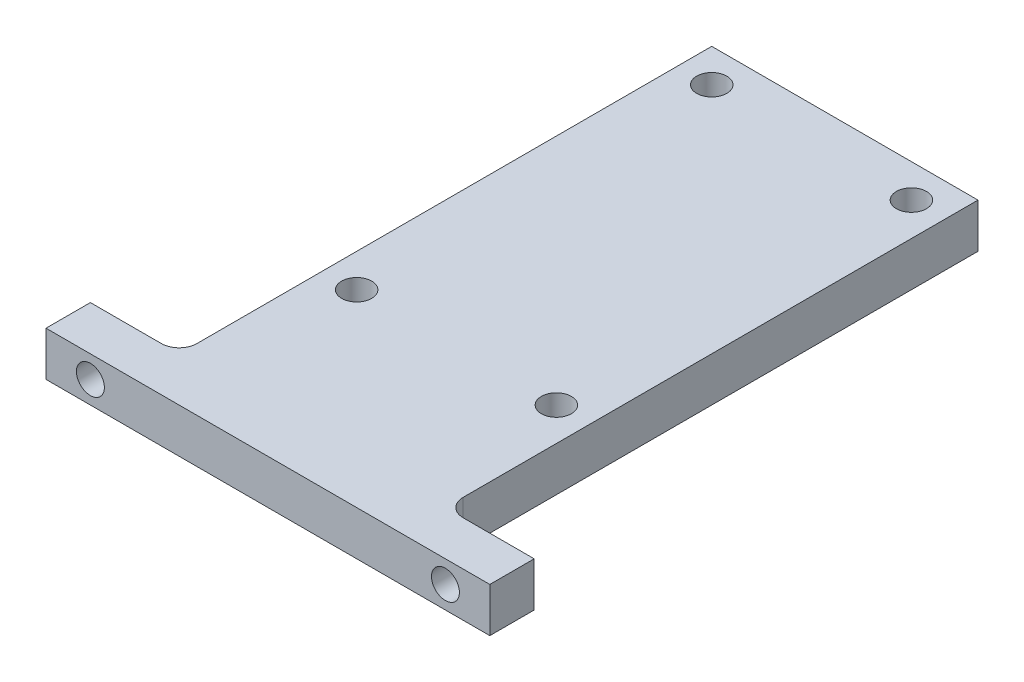
SolidWorks part; units mm, degrees
ref_plane "Front Plane" through (0, 0, 0) normal (0, 0, 1) x (1, 0, 0)
ref_plane "Top Plane" through (0, 0, 0) normal (0, 1, 0) x (1, 0, 0)
ref_plane "Right Plane" through (0, 0, 0) normal (1, 0, 0) x (0, 0, -1)
sketch "Sketch1" plane through (0, 0, 0) normal (0, 1, 0) x (1, 0, 0)
  line L0 (0, 0) -> (63.5, 0)
  line L1 (63.5, 0) -> (63.5, 6.35)
  line L2 (63.5, 6.35) -> (50.8, 6.35)
  line L3 (50.8, 6.35) -> (50.8, 82.55)
  line L4 (50.8, 82.55) -> (12.7, 82.55)
  line L5 (12.7, 82.55) -> (12.7, 6.35)
  line L6 (12.7, 6.35) -> (0, 6.35)
  line L7 (0, 6.35) -> (0, 0)
  dimension "D1" = 12.7
  dimension "D2" = 38.1
  dimension "D3" = 76.2
  dimension "D4" = 6.35
extrude "Boss-Extrude1" add sketch "Sketch1" along normal blind 6.35
sketch "Sketch2" plane through (0, 0, 0) normal (0, 0, 1) x (1, 0, 0)
  line L0 (0, 6.35) -> (0, 0) construction
  line L1 (12.7, 6.35) -> (0, 6.35) construction
  line L2 (63.5, 6.35) -> (50.8, 6.35) construction
  circle A0 centre (6.35, 3.175) radius 2
  circle A1 centre (57.15, 3.175) radius 2
  point P7 (0, 3.175)
  point P11 (6.35, 6.35)
  point P15 (57.15, 6.35)
  dimension "D1" = 4
extrude "Cut-Extrude1" cut sketch "Sketch2" against normal through all both and the other way through all
sketch "Sketch3" plane through (0, 6.35, 0) normal (0, 1, 0) x (1, 0, 0)
  line L3 (12.7, 82.55) -> (12.7, 6.35) construction
  line L4 (50.8, 82.55) -> (12.7, 82.55) construction
  point P0 (17.4625, 77.7875)
  point P5 (17.4625, 26.9875)
  point P6 (46.0375, 77.7875)
  point P7 (46.0375, 26.9875)
  point P8 (0, 0)
  point P9 (0, 0)
  point P10 (0, 0)
  dimension "D1" = 4.7625
  dimension "D2" = 4.7625
  dimension "D3" = 50.8
  dimension "D4" = 28.575
fillet "Fillet1" radius 2.54 2 edges at (12.7, 3.175, -6.35) (50.8, 3.175, -6.35)
hole_wizard "M4 Clearance Hole1" positions "Sketch4" profile "Sketch5" hole size "M4" standard "ANSI Metric" end condition through all
sketch "Sketch4" plane through (0, 6.35, 0) normal (0, 1, 0) x (1, 0, 0)
  point P0 (17.4625, 77.7875)
  point P3 (46.0375, 77.7875)
  point P6 (46.0375, 26.9875)
  point P9 (17.4625, 26.9875)
sketch "Sketch5" plane through (17.4625, 6.35, -77.7875) normal (1, 0, 0) x (0, 0, 1)
  line L0 (0, 0) -> (0, 6.35)
  line L1 (0, 6.35) -> (2.15, 6.35)
  line L2 (2.15, 6.35) -> (2.15, 0)
  line L5 (2.15, 0) -> (0, 0)
  line L11 (0, -6.35) -> (0, 107.95) construction
  dimension "Thru Hole Dia." = 4.3
  dimension "Thru Hole Depth" = 6.35
